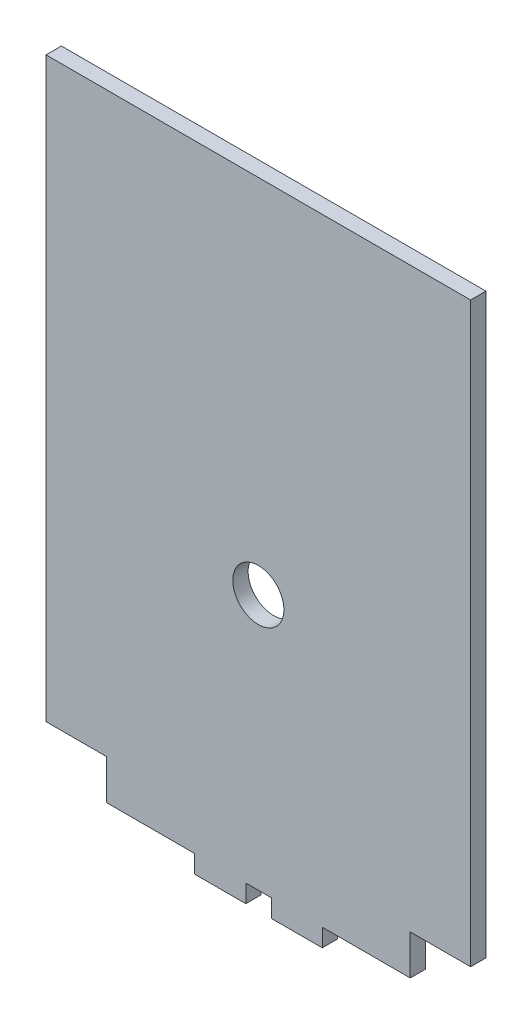
SolidWorks part; units mm, degrees
ref_plane "Alzado" through (0, 0, 0) normal (0, 0, 1) x (1, 0, 0)
ref_plane "Planta" through (0, 0, 0) normal (0, 1, 0) x (1, 0, 0)
ref_plane "Vista lateral" through (0, 0, 0) normal (1, 0, 0) x (0, 0, -1)
sketch "Model" plane through (0, 0, 0) normal (0, 0, 1) x (1, 0, 0)
  line L0 (51.4522, -12.8451) -> (64.2916, -12.8451)
  line L1 (38.6233, -12.8451) -> (51.4522, -12.8451)
  line L2 (10.1522, -40.5371) -> (10.1522, -12.8451)
  line L3 (10.1522, -12.8451) -> (38.6233, -12.8451)
  line L4 (81.3522, -125.7451) -> (93.1522, -125.7451)
  line L5 (81.3522, -133.542) -> (81.3522, -125.7451)
  line L6 (10.1522, -125.7451) -> (21.9522, -125.7451)
  line L7 (21.9522, -125.7451) -> (21.9522, -133.5355)
  line L8 (93.1522, -12.8451) -> (64.2916, -12.8451)
  line L9 (93.1522, -125.7451) -> (93.1522, -12.8451)
  line L10 (64.1522, -133.5374) -> (81.3522, -133.542)
  line L11 (64.1522, -137.0374) -> (64.1522, -133.5374)
  line L12 (54.2022, -137.0374) -> (64.1522, -137.0374)
  line L13 (54.2022, -133.5374) -> (54.2022, -137.0374)
  line L14 (49.2022, -133.5374) -> (54.2022, -133.5374)
  line L15 (49.2022, -137.0374) -> (49.2022, -133.5374)
  line L16 (39.1522, -137.0374) -> (49.2022, -137.0374)
  line L17 (39.1522, -133.5439) -> (39.1522, -137.0374)
  line L18 (21.9522, -133.5355) -> (39.1522, -133.5439)
  line L19 (10.1522, -40.5371) -> (10.1522, -125.7451)
  circle A0 centre (51.6522, -83.5451) radius 5
extrude "Saliente-Extruir1" add sketch "Model" along normal blind 3
